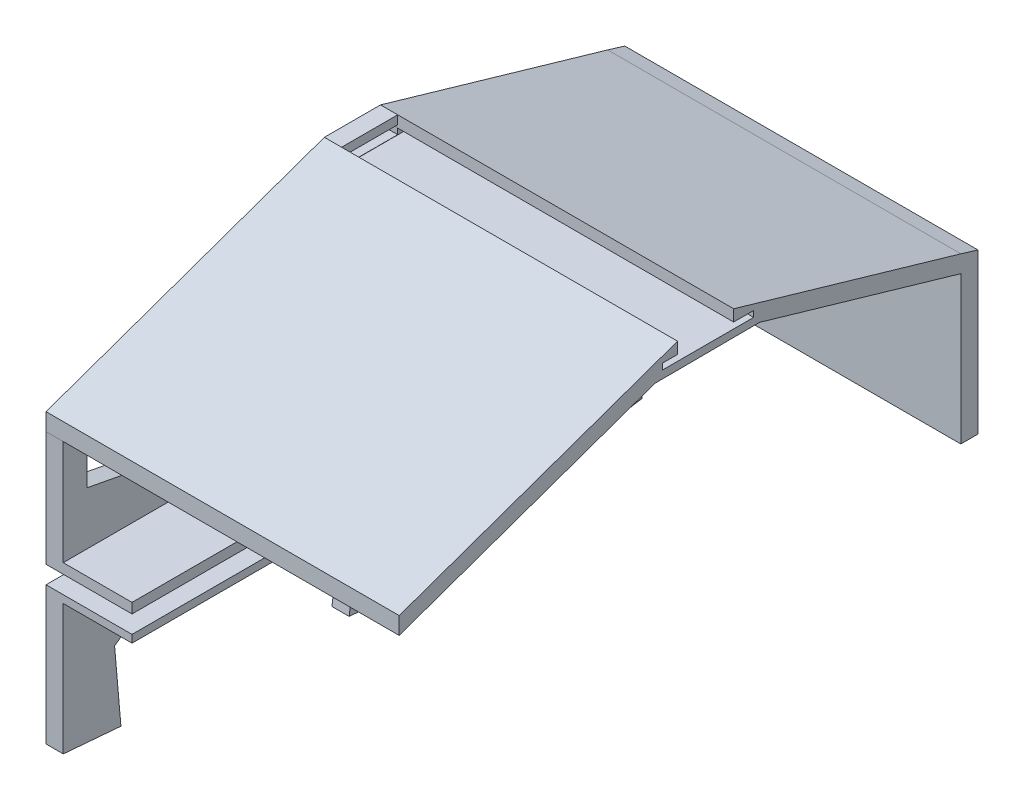
SolidWorks part; units mm, degrees
ref_plane "Front Plane" through (0, 0, 0) normal (0, 0, 1) x (1, 0, 0)
ref_plane "Top Plane" through (0, 0, 0) normal (0, 1, 0) x (1, 0, 0)
ref_plane "Right Plane" through (0, 0, 0) normal (1, 0, 0) x (0, 0, -1)
sketch "Sketch1" plane through (0, 0, 0) normal (1, 0, 0) x (0, 0, -1)
  line L7 (0, 117.5774) -> (159.1764, 117.5774) construction
  line L9 (-123.5256, 81.219) -> (-123.5256, 117.5774) construction
  line L11 (-123.5256, 117.5774) -> (-31.374, 117.5774) construction
  line L12 (159.1764, 71.351) -> (159.1764, 117.5774) construction
  line L22 (-123.5256, 81.219) -> (-123.5256, -25.0829)
  line L51 (5.2018, 40.001) -> (77.5282, 55.0563)
  line L52 (77.5282, 55.0563) -> (77.5282, 85.8304)
  line L55 (-123.5256, -25.0829) -> (-102.221, -26.86)
  line L56 (-102.221, -26.86) -> (-104.557, 0)
  line L57 (-104.557, 0) -> (-79.6468, 17.6863)
  line L58 (-79.6468, 17.6863) -> (-41.0945, 17.6863)
  line L59 (-41.0945, 17.6863) -> (-13.7798, -3.6413)
  line L60 (-13.7798, -3.6413) -> (-17.9475, -33.8894)
  line L61 (-17.9475, -33.8894) -> (-12.5619, -34.3386)
  line L67 (-79.6468, 84.2241) -> (-79.6468, 48.574)
  line L76 (-79.6468, 84.2241) -> (-20.7359, 105.0152)
  line L77 (-20.7359, 105.0152) -> (0, 105.0152)
  line L78 (0, 105.0152) -> (0, 40.0073)
  line L79 (5.2018, 40.001) -> (5.2018, 105.0152)
  line L80 (5.2018, 105.0152) -> (77.5282, 85.8304)
  line L81 (0, 40.0073) -> (-79.6468, 48.574)
  line L82 (-86.0905, 81.219) -> (-86.0905, 50.1978)
  line L85 (-86.0905, 81.219) -> (-114.76, 71.351)
  line L87 (-114.76, 71.351) -> (-114.76, 55.6667)
  line L88 (-114.76, 55.6667) -> (-86.0905, 50.1978)
  line L89 (-123.5256, 81.219) -> (-20.7359, 117.5774)
  line L93 (-20.7359, 111.2274) -> (0, 111.2274)
  line L94 (0, 111.2274) -> (0, 114.4024)
  line L97 (77.5282, 75.5815) -> (77.5282, 66.8423) construction
  line L100 (0, 117.5774) -> (90.2282, 91.2816)
  line L104 (90.2282, 59.8949) -> (90.2282, -12.9615) construction
  line L105 (-0.017, 117.4897) -> (159.1594, 71.2633) construction
  line L106 (90.2282, 91.2816) -> (90.2282, -18.3031)
  line L107 (-12.5789, -34.4263) -> (159.1594, -7.4926) construction
  line L108 (90.2282, -18.3031) -> (-12.5619, -34.3386)
  line L110 (-20.7359, 114.4024) -> (-20.7359, 111.2274) construction
  line L111 (-20.7359, 114.4024) -> (0, 114.4024)
  line L112 (-20.7359, 117.5774) -> (0, 117.5774)
  line L113 (-20.7359, 114.4024) -> (-20.7359, 111.2274)
  dimension "D1" = 3.175
  dimension "D2" = 6.35
  dimension "D4" = 20.7359
extrude "Boss-Extrude1" add sketch "Sketch1" along normal blind 6.35
sketch "Sketch2" plane through (6.35, 0, 0) normal (1, 0, 0) x (0, 0, -1)
  line L33 (-123.5256, 81.219) -> (-123.5256, -25.0829) construction
  line L38 (159.1764, -7.4049) -> (159.1764, 71.351) construction
  line L39 (159.1764, 25.8619) -> (76.5252, 25.8619)
  line L40 (159.1764, 25.8619) -> (159.1764, 32.3891)
  line L41 (159.1764, 32.3891) -> (76.5252, 32.3891)
  line L42 (76.5252, 25.8619) -> (76.5252, 32.3891)
  line L44 (-123.5256, 32.4659) -> (-123.5256, 25.8619)
  line L46 (-46.5558, 32.4659) -> (-46.5558, 25.8619)
  line L47 (-123.5256, 32.4659) -> (-46.5558, 32.4659)
  line L48 (-46.5558, 25.8619) -> (-123.5256, 25.8619)
  dimension "D3" = 6.5272
  dimension "D4" = 6.604
extrude "Cut-Extrude1" cut sketch "Sketch2" against normal through all
sketch "Sketch4" plane through (6.35, 0, 0) normal (1, 0, 0) x (0, 0, -1)
  line L1 (-123.5256, 81.2474) -> (-123.5256, -26.2693) construction
  line L2 (-123.5256, 35.1881) -> (158.7607, 35.1881)
  line L3 (-123.5256, 35.1881) -> (-123.5256, 23.3267)
  line L4 (-123.5256, 23.3267) -> (158.7607, 23.3267)
  line L5 (158.7607, 35.1881) -> (158.7607, 23.3267)
sketch "Sketch5" plane through (6.35, 0, 0) normal (1, 0, 0) x (0, 0, -1)
  line L2 (-0.017, 117.4897) -> (159.1594, 117.4897) construction
  line L4 (159.1594, -7.4926) -> (159.1594, 71.2633)
  line L5 (-123.5426, 81.1313) -> (-123.5426, 117.4897) construction
  line L6 (-123.5426, 117.4897) -> (-31.391, 117.4897) construction
  line L9 (159.1594, 71.2633) -> (159.1594, 117.4897) construction
  line L10 (-123.5426, 81.1313) -> (-123.5426, -25.1706)
  line L11 (5.1849, 39.9134) -> (77.5113, 54.9686)
  line L30 (77.5113, 54.9686) -> (77.5113, 85.7427)
  line L31 (-12.5789, -34.4263) -> (159.1594, -7.4926)
  line L32 (-123.5426, -25.1706) -> (-102.238, -26.9477)
  line L33 (-102.238, -26.9477) -> (-104.574, -0.0877)
  line L34 (-104.574, -0.0877) -> (-79.6638, 17.5986)
  line L35 (-79.6638, 17.5986) -> (-41.1115, 17.5986)
  line L36 (-41.1115, 17.5986) -> (-13.7968, -3.729)
  line L37 (-13.7968, -3.729) -> (-17.9645, -33.9771)
  line L38 (-17.9645, -33.9771) -> (-12.5789, -34.4263)
  line L39 (-79.6638, 84.1365) -> (-79.6638, 48.4864)
  line L40 (-79.6638, 84.1365) -> (-20.7529, 104.9275)
  line L41 (-20.7529, 104.9275) -> (-0.017, 104.9275)
  line L42 (-0.017, 104.9275) -> (-0.017, 39.9196)
  line L43 (5.1849, 39.9134) -> (5.1849, 104.9275)
  line L44 (5.1849, 104.9275) -> (77.5113, 85.7427)
  line L45 (-0.017, 39.9196) -> (-79.6638, 48.4864)
  line L46 (-86.1075, 81.1313) -> (-86.1075, 50.1101)
  line L47 (-86.1075, 81.1313) -> (-114.777, 71.2633)
  line L48 (-114.777, 71.2633) -> (-114.777, 55.579)
  line L49 (-114.777, 55.579) -> (-86.1075, 50.1101)
  line L50 (-123.5426, 81.1313) -> (-20.7529, 117.4897)
  line L51 (-0.017, 117.4897) -> (159.1594, 71.2633)
  line L52 (-20.7529, 117.4897) -> (-20.7529, 111.1397)
  line L53 (-20.7529, 111.1397) -> (-0.017, 111.1397)
  line L54 (-0.017, 111.1397) -> (-0.017, 117.4897)
  dimension "D1" = 6.35
sketch "Sketch6" plane through (0, 0, 0) normal (-1, 0, 0) x (0, 0, 1)
  line L0 (123.5256, 81.219) -> (123.5256, 32.4659) construction
  line L1 (-82.9764, 32.3891) -> (123.5256, 32.3891)
  line L3 (-82.9764, 36.1008) -> (123.5256, 36.1008)
  line L4 (123.5256, 32.3891) -> (123.5256, 36.1008)
  line L5 (123.5256, 25.8619) -> (123.5256, -25.0829) construction
  line L6 (-82.9764, 25.8619) -> (123.5256, 25.8619)
  line L8 (-82.9764, 23.0456) -> (123.5256, 23.0456)
  line L9 (123.5256, 25.8619) -> (123.5256, 23.0456)
  line L10 (-82.9764, 25.8619) -> (-82.9764, 23.0456)
  line L12 (-82.9764, 36.1008) -> (-82.9764, 32.3891)
extrude "Boss-Extrude3" add sketch "Sketch6" against normal blind 31.75
sketch "Sketch8" plane through (0, 0, 0) normal (-1, 0, 0) x (0, 0, 1)
  line L0 (0, 117.5774) -> (-83.8782, 93.2183)
  line L5 (0, 117.5774) -> (0.0112, 113.3442)
  line L7 (0.017, 111.1397) -> (20.7529, 111.1397)
  line L10 (123.5426, 81.1313) -> (123.5426, -25.1706) construction
  line L12 (123.5426, 74.869) -> (29.0978, 108.2701)
  line L22 (-9.5252, 108.4612) -> (29.0978, 108.2701)
  line L26 (123.5426, 74.869) -> (123.5256, 81.219)
  line L27 (123.5256, 81.219) -> (20.7359, 117.5774)
  line L30 (26.2283, 113.3442) -> (26.2283, 111.1397)
  line L33 (-83.8782, 93.2183) -> (-90.2282, 91.2816)
  line L34 (0.017, 117.4897) -> (-159.1594, 71.2633) construction
  line L35 (-90.2282, 32.3891) -> (-90.2282, 91.2816) construction
  line L36 (-90.2282, 91.2816) -> (-90.2282, 32.3891)
  line L38 (26.2283, 113.3442) -> (20.7529, 113.3442)
  line L40 (-90.2282, 32.3891) -> (-83.8782, 32.3891)
  line L41 (-90.2282, 32.3891) -> (-82.9764, 32.3891) construction
  line L43 (-83.8782, 93.2183) -> (-83.8782, 86.8683) construction
  line L44 (-83.8782, 32.3891) -> (-83.8782, 86.8683)
  line L45 (-83.8782, 86.8683) -> (-9.5252, 108.4612)
  line L46 (0.017, 111.1397) -> (-7.3776, 111.1397)
  line L47 (-7.3776, 111.1397) -> (-7.3776, 113.3442)
  line L48 (-7.3776, 113.3442) -> (0.0112, 113.3442)
  line L50 (26.2283, 111.1397) -> (20.7529, 111.1397)
  line L51 (20.7529, 117.4897) -> (20.7529, 111.1397) construction
  line L52 (20.7529, 113.3442) -> (20.7359, 117.5774)
  dimension "D1" = 6.35
  dimension "D2" = 6.35
extrude "Boss-Extrude5" add sketch "Sketch8" against normal blind 130.429
